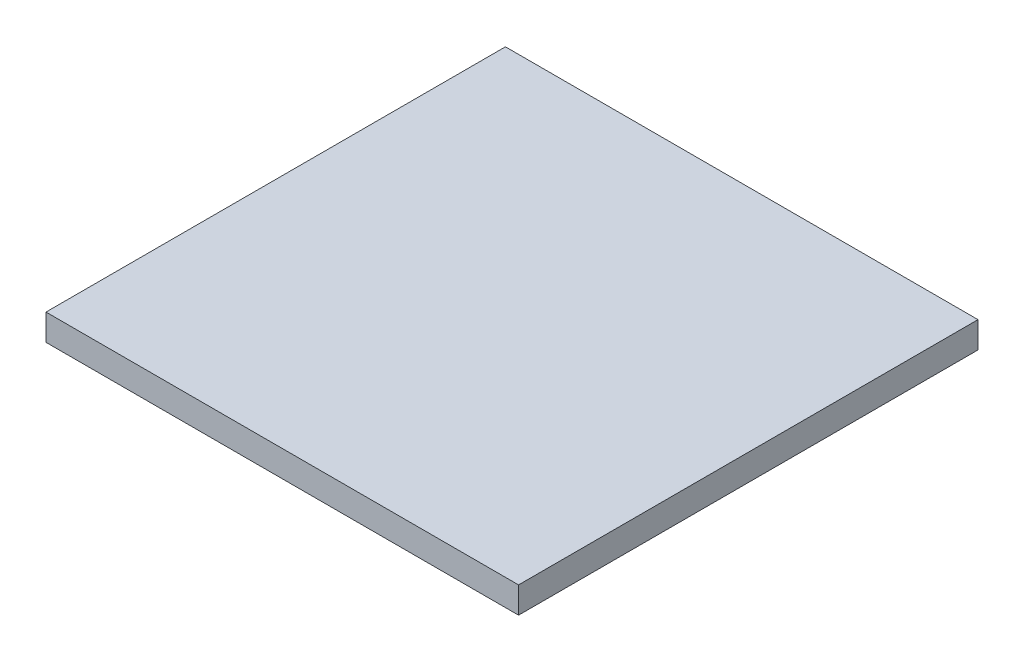
SolidWorks part; units mm, degrees
ref_plane "Front Plane" through (0, 0, 0) normal (0, 0, 1) x (1, 0, 0)
ref_plane "Top Plane" through (0, 0, 0) normal (0, 1, 0) x (1, 0, 0)
ref_plane "Right Plane" through (0, 0, 0) normal (1, 0, 0) x (0, 0, -1)
sketch "Sketch1" plane through (0, 0, 0) normal (0, 1, 0) x (1, 0, 0)
  line L1 (0, 0) -> (36, 0)
  line L2 (0, 0) -> (0, -35)
  line L3 (0, -35) -> (36, -35)
  line L4 (36, 0) -> (36, -35)
  dimension "D1" = 36
  dimension "D2" = 35
extrude "Boss-Extrude1" add sketch "Sketch1" along normal blind 2
